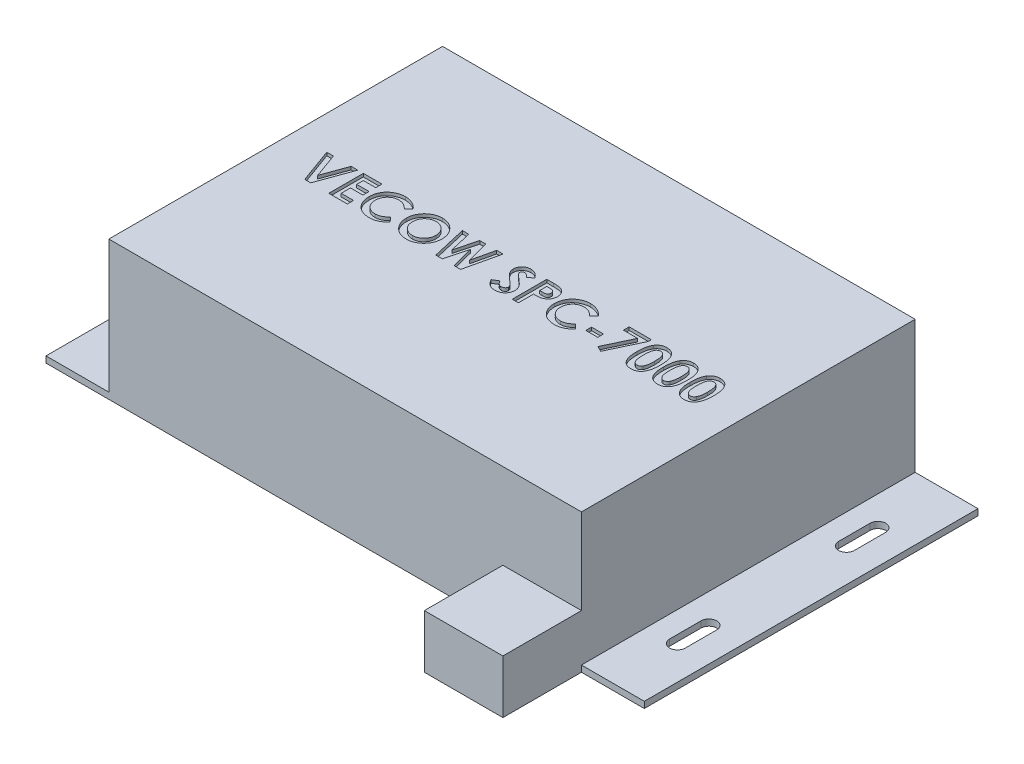
SolidWorks part; units mm, degrees
ref_plane "Front Plane" through (0, 0, 0) normal (0, 0, 1) x (1, 0, 0)
ref_plane "Top Plane" through (0, 0, 0) normal (0, 1, 0) x (1, 0, 0)
ref_plane "Right Plane" through (0, 0, 0) normal (1, 0, 0) x (0, 0, -1)
sketch "Sketch1" plane through (0, 0, 0) normal (0, 1, 0) x (1, 0, 0)
  line L1 (-75.2, 53.1) -> (75.2, 53.1)
  line L2 (-75.2, 53.1) -> (-75.2, -53.1)
  line L3 (-75.2, -53.1) -> (75.2, -53.1)
  line L4 (75.2, 53.1) -> (75.2, -53.1)
  line L5 (-75.2, 53.1) -> (75.2, -53.1) construction
  line L6 (-75.2, -53.1) -> (75.2, 53.1) construction
  point P0 (0, 0)
  dimension "D1" = 150.4
  dimension "D2" = 106.2
extrude "Boss-Extrude1" add sketch "Sketch1" along normal blind 44.2
sketch "Sketch2" plane through (75.2, 0, 0) normal (1, 0, 0) x (0, 0, -1)
  line L0 (53.1, 44.2) -> (53.1, 0) construction
  line L1 (-53.1, 0) -> (53.1, 0)
  line L2 (-53.1, 0) -> (-53.1, 2)
  line L3 (-53.1, 2) -> (53.1, 2)
  line L4 (53.1, 0) -> (53.1, 2)
  dimension "D1" = 2
extrude "Boss-Extrude2" add sketch "Sketch2" along normal blind 20
mirror "Mirror1" about plane through (0, 0, 0) normal (1, 0, 0) of "Boss-Extrude2"
sketch "Sketch3" plane through (0, 0, 0) normal (0, -1, 0) x (1, 0, 0)
  line L0 (-84.55, 31.9) -> (-84.55, 21.9) construction
  line L1 (-82.05, 31.9) -> (-82.05, 21.9)
  line L2 (-87.05, 31.9) -> (-87.05, 21.9)
  line L3 (-84.55, -21.9) -> (-84.55, -31.9) construction
  line L4 (-82.05, -21.9) -> (-82.05, -31.9)
  line L5 (-84.55, 26.9) -> (84.55, 26.9) construction
  line L6 (-84.55, 26.9) -> (-84.55, -26.9) construction
  line L7 (-84.55, -26.9) -> (84.55, -26.9) construction
  line L8 (84.55, 26.9) -> (84.55, -26.9) construction
  line L9 (-84.55, 26.9) -> (84.55, -26.9) construction
  line L10 (-84.55, -26.9) -> (84.55, 26.9) construction
  line L11 (-87.05, -21.9) -> (-87.05, -31.9)
  line L12 (84.55, 31.9) -> (84.55, 21.9) construction
  line L13 (87.05, 31.9) -> (87.05, 21.9)
  line L14 (82.05, 31.9) -> (82.05, 21.9)
  line L15 (84.55, -21.9) -> (84.55, -31.9) construction
  line L16 (87.05, -21.9) -> (87.05, -31.9)
  line L17 (82.05, -21.9) -> (82.05, -31.9)
  arc A0 (-82.05, 31.9) -> (-87.05, 31.9) centre (-84.55, 31.9) ccw
  arc A1 (-87.05, 21.9) -> (-82.05, 21.9) centre (-84.55, 21.9) ccw
  arc A2 (-82.05, -21.9) -> (-87.05, -21.9) centre (-84.55, -21.9) ccw
  arc A3 (-87.05, -31.9) -> (-82.05, -31.9) centre (-84.55, -31.9) ccw
  arc A4 (87.05, 31.9) -> (82.05, 31.9) centre (84.55, 31.9) ccw
  arc A5 (82.05, 21.9) -> (87.05, 21.9) centre (84.55, 21.9) ccw
  arc A6 (87.05, -21.9) -> (82.05, -21.9) centre (84.55, -21.9) ccw
  arc A7 (82.05, -31.9) -> (87.05, -31.9) centre (84.55, -31.9) ccw
  point P0 (0, 0)
  point P7 (-84.55, 26.9)
  point P14 (-84.55, -26.9)
  point P22 (84.55, 26.9)
  point P29 (84.55, -26.9)
  dimension "D3" = 2.5
  dimension "D1" = 169.1
  dimension "D2" = 53.8
  dimension "D4" = 10
extrude "Cut-Extrude1" cut sketch "Sketch3" against normal blind 20
sketch "Sketch4" plane through (0, 44.2, 0) normal (0, 1, 0) x (1, 0, 0)
  line L0 (-75.2, -5.5) -> (75.2, -5.5) construction
  line L1 (-75.2, 53.1) -> (-75.2, -53.1) construction
  line L2 (75.2, 53.1) -> (75.2, -53.1) construction
  text T0 "VECOW SPC-7000" font "Century Gothic" height 11
  dimension "D1" = 5.5
extrude "Cut-Extrude2" cut sketch "Sketch4" against normal blind 1
sketch "Sketch5" plane through (0, 0, -53.1) normal (0, 0, -1) x (-1, 0, 0)
  line L0 (-75.2, 44.2) -> (75.2, 44.2) construction
  line L1 (-68.2, 37.2) -> (68.2, 37.2)
  line L2 (-68.2, 37.2) -> (-68.2, 9)
  line L3 (-68.2, 9) -> (68.2, 9)
  line L4 (68.2, 37.2) -> (68.2, 9)
  line L5 (-68.2, 37.2) -> (68.2, 9) construction
  line L6 (-68.2, 9) -> (68.2, 37.2) construction
  line L7 (-75.2, 44.2) -> (-75.2, 2) construction
  line L8 (75.2, 44.2) -> (75.2, 2) construction
  point P0 (0, 23.1)
  point P7 (0, 44.2)
  point P10 (-75.2, 23.1)
  dimension "D1" = 7
  dimension "D2" = 7
extrude "Boss-Extrude3" [suppressed] add sketch "Sketch5" along normal blind 50
sketch "Sketch6" plane through (0, 0, 53.1) normal (0, 0, 1) x (1, 0, 0)
  line L0 (-95.2, 0) -> (95.2, 0) construction
  line L1 (75.2, 0) -> (50.2, 0)
  line L2 (75.2, 0) -> (75.2, 17)
  line L3 (75.2, 17) -> (50.2, 17)
  line L4 (50.2, 0) -> (50.2, 17)
  dimension "D1" = 25
  dimension "D2" = 17
extrude "Boss-Extrude4" add sketch "Sketch6" along normal blind 25
